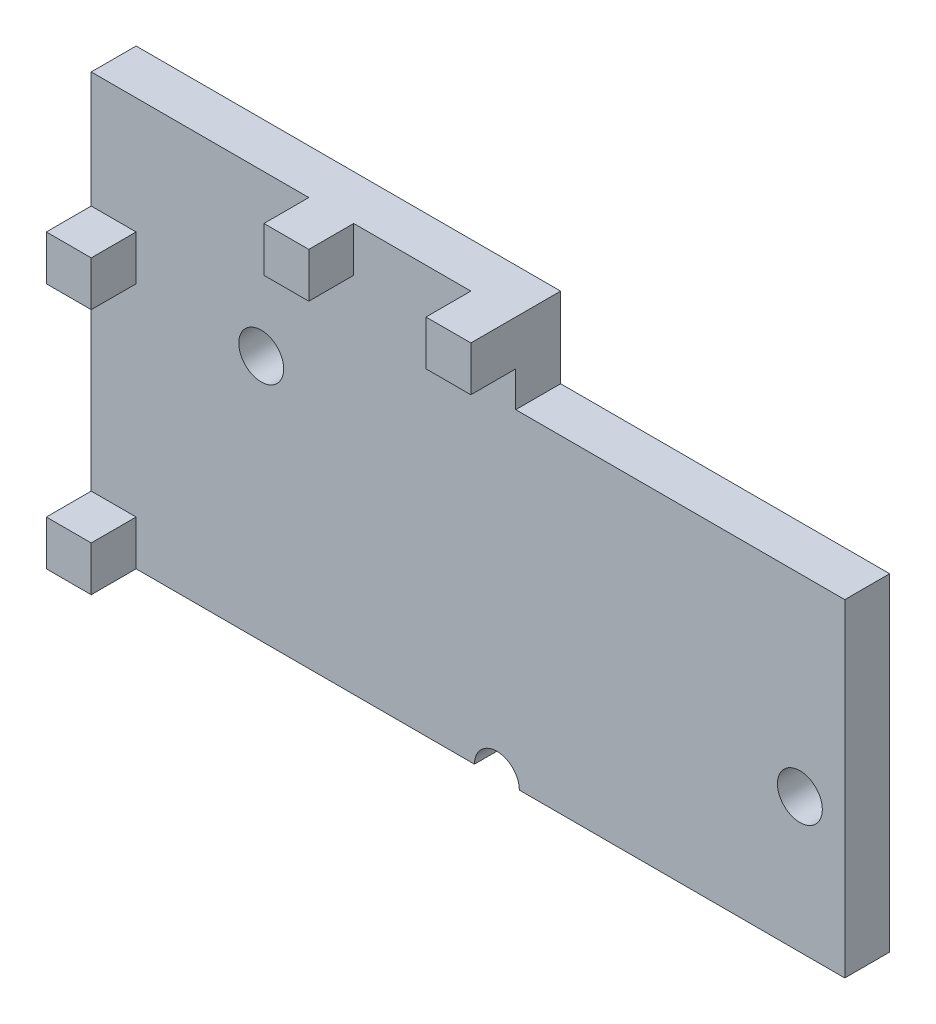
SolidWorks part; units mm, degrees
ref_plane "Front Plane" through (0, 0, 0) normal (0, 0, 1) x (1, 0, 0)
ref_plane "Top Plane" through (0, 0, 0) normal (0, 1, 0) x (1, 0, 0)
ref_plane "Right Plane" through (0, 0, 0) normal (1, 0, 0) x (0, 0, -1)
sketch "Sketch1" plane through (0, 0, 0) normal (0, 0, 1) x (1, 0, 0)
  line L0 (-0.75, -3.25) -> (-7.5, -3.25)
  line L1 (7.5, 3.25) -> (-7.5, 3.25)
  line L2 (7.5, 3.25) -> (7.5, -3.25)
  line L3 (7.5, -3.25) -> (0.25, -3.25)
  line L4 (-7.5, 3.25) -> (-7.5, -3.25)
  line L5 (7.5, 3.25) -> (-7.5, -3.25) construction
  line L6 (7.5, -3.25) -> (-7.5, 3.25) construction
  circle A0 centre (-5.5, 2.25) radius 0.5
  circle A1 centre (6.5, -0.25) radius 0.5
  arc A2 (0.25, -3.25) -> (-0.75, -3.25) centre (-0.25, -3.25) ccw
  point P0 (0, 0)
  dimension "D3" = 1
  dimension "D4" = 1
  dimension "D5" = 2
  dimension "D6" = 1
  dimension "D7" = 3
  dimension "D1" = 15
  dimension "D2" = 6.5
  dimension "D8" = 7.75
extrude "Front Face Ext" add sketch "Sketch1" along normal blind 1
sketch "Sketch2" plane through (-7.5, 0, 0) normal (-1, 0, 0) x (0, 0, 1)
  line L1 (0, 3.25) -> (1, 3.25)
  line L2 (0, 3.25) -> (0, -3.25)
  line L3 (0, -3.25) -> (1, -3.25)
  line L4 (1, 3.25) -> (1, -3.25)
extrude "Length-Extrude1" add sketch "Sketch2" along normal blind 1.7874
sketch "Sketch3" plane through (0, 0, 1) normal (0, 0, 1) x (1, 0, 0)
  line L2 (-9.2874, 3.25) -> (-8.2874, 3.25)
  line L3 (-9.2874, 3.25) -> (-9.2874, 2.25)
  line L4 (-9.2874, 2.25) -> (-8.2874, 2.25)
  line L5 (-8.2874, 3.25) -> (-8.2874, 2.25)
  line L6 (-9.2874, -3.25) -> (-8.2874, -3.25)
  line L7 (-9.2874, -3.25) -> (-9.2874, -2.25)
  line L8 (-9.2874, -2.25) -> (-8.2874, -2.25)
  line L9 (-8.2874, -3.25) -> (-8.2874, -2.25)
  dimension "D1" = 1
  dimension "D2" = 1
extrude "Boss-Extrude2" add sketch "Sketch3" along normal blind 1
sketch "Sketch4" plane through (0, 3.25, 0) normal (0, 1, 0) x (1, 0, 0)
  line L1 (0.17, -1) -> (-9.2874, -1)
  line L2 (0.17, -1) -> (0.17, 0)
  line L3 (0.17, 0) -> (-9.2874, 0)
  line L4 (-9.2874, -1) -> (-9.2874, 0)
  line L5 (7.5, -1) -> (7.5, 0) construction
  dimension "D1" = 7.33
extrude "Height-Extrude3" add sketch "Sketch4" along normal blind 2.5874
sketch "Sketch5" plane through (0, 0, 1) normal (0, 0, 1) x (1, 0, 0)
  line L0 (7.5, -3.25) -> (7.5, 3.25) construction
  line L1 (0.17, 5.8374) -> (-0.83, 5.8374)
  line L2 (0.17, 5.8374) -> (0.17, 4.8374)
  line L3 (0.17, 4.8374) -> (-0.83, 4.8374)
  line L4 (-0.83, 5.8374) -> (-0.83, 4.8374)
  line L5 (-9.2874, 5.8374) -> (0.17, 5.8374) construction
  line L7 (-3.44, 5.8374) -> (-4.44, 5.8374)
  line L8 (-3.44, 5.8374) -> (-3.44, 4.8374)
  line L9 (-3.44, 4.8374) -> (-4.44, 4.8374)
  line L10 (-4.44, 5.8374) -> (-4.44, 4.8374)
  dimension "D1" = 7.33
  dimension "D2" = 4.61
extrude "Boss-Extrude4" add sketch "Sketch5" along normal blind 1
sketch "Sketch6" plane through (0, 3.25, 0) normal (0, 1, 0) x (1, 0, 0)
  line L1 (0.17, -1) -> (7.5, -1)
  line L2 (0.17, -1) -> (0.17, 0)
  line L3 (0.17, 0) -> (7.5, 0)
  line L4 (7.5, -1) -> (7.5, 0)
extrude "Boss-Extrude5" add sketch "Sketch6" along normal blind 0.8
